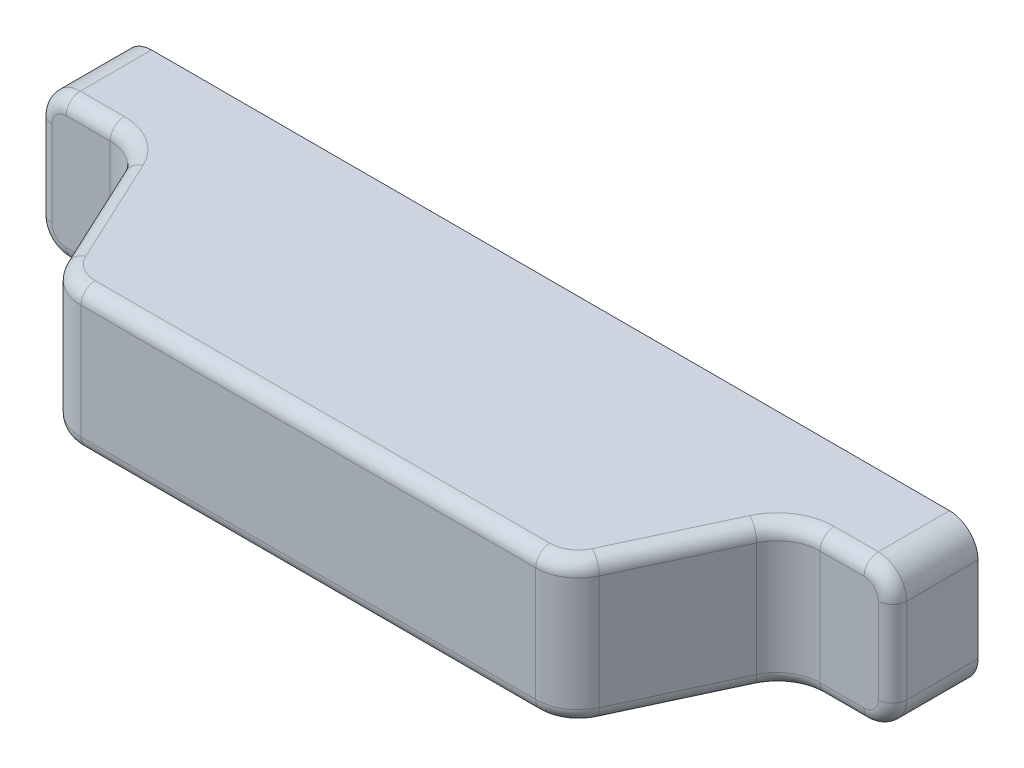
SolidWorks part; units mm, degrees
ref_plane "Front Plane" through (0, 0, 0) normal (0, 0, 1) x (1, 0, 0)
ref_plane "Top Plane" through (0, 0, 0) normal (0, 1, 0) x (1, 0, 0)
ref_plane "Right Plane" through (0, 0, 0) normal (1, 0, 0) x (0, 0, -1)
sketch "Sketch1" plane through (0, 0, 0) normal (0, 0, 1) x (1, 0, 0)
  line L1 (-119, -97.7573) -> (-59, -97.7573)
  line L2 (-119, -97.7573) -> (-119, -87.7573)
  line L3 (-119, -87.7573) -> (-59, -87.7573)
  line L4 (-59, -97.7573) -> (-59, -87.7573)
  line L7 (-89, -7.4927) -> (-89, -172.4927) construction
  dimension "D1" = 30
  dimension "D2" = 60
extrude "Boss-Extrude1" add sketch "Sketch1" along normal blind 17
sketch "Sketch2" plane through (0, -97.7573, 0) normal (0, -1, 0) x (1, 0, 0)
  line L0 (-106.8706, 17) -> (-112, 6)
  line L1 (-119, 17) -> (-59, 17) construction
  line L2 (-112, 6) -> (-119, 6)
  line L3 (-119, 17) -> (-119, 0) construction
  line L4 (-119, 0) -> (-59, 0) construction
  line L5 (-119, 6) -> (-119, 17)
  line L6 (-119, 17) -> (-106.8706, 17)
  line L7 (-89, 0) -> (-89, 17) construction
  line L8 (-104, 17) -> (-74, 17) construction
  line L9 (-59, 17) -> (-71.1294, 17)
  line L10 (-59, 6) -> (-59, 17)
  line L11 (-66, 6) -> (-59, 6)
  line L12 (-71.1294, 17) -> (-66, 6)
  dimension "D1" = 6
  dimension "D2" = 7
  dimension "D3" = 115
extrude "Cut-Extrude1" cut sketch "Sketch2" against normal up to surface (10 mm away)
fillet "Fillet1" radius 3
fillet "Fillet2" radius 2
fillet "Fillet3" radius 1
